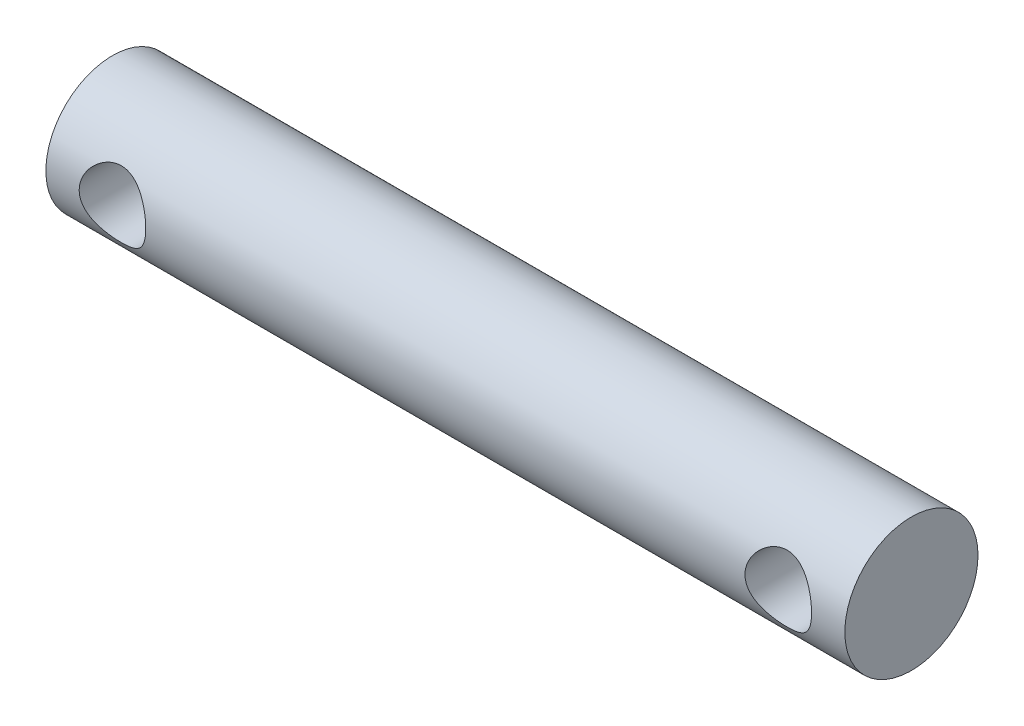
SolidWorks part; units mm, degrees
ref_plane "前基準面" through (0, 0, 0) normal (0, 0, 1) x (1, 0, 0)
ref_plane "上基準面" through (0, 0, 0) normal (0, 1, 0) x (1, 0, 0)
ref_plane "右基準面" through (0, 0, 0) normal (1, 0, 0) x (0, 0, -1)
sketch "草圖1" plane through (0, 0, 0) normal (1, 0, 0) x (0, 0, -1)
  circle A0 centre (0, 0) radius 3
  dimension "D1" = 6
extrude "填料-伸長1" add sketch "草圖1" along normal blind 36
sketch "草圖2" plane through (0, 0, 0) normal (0, 0, 1) x (1, 0, 0)
  line L0 (36, -3) -> (36, 3) construction
  circle A0 centre (3, 0) radius 1.5
  circle A1 centre (33, 0) radius 1.5
  dimension "D1" = 3
  dimension "D2" = 3
  dimension "D3" = 30
extrude "除料-伸長1" cut sketch "草圖2" against normal through all both and the other way through all
